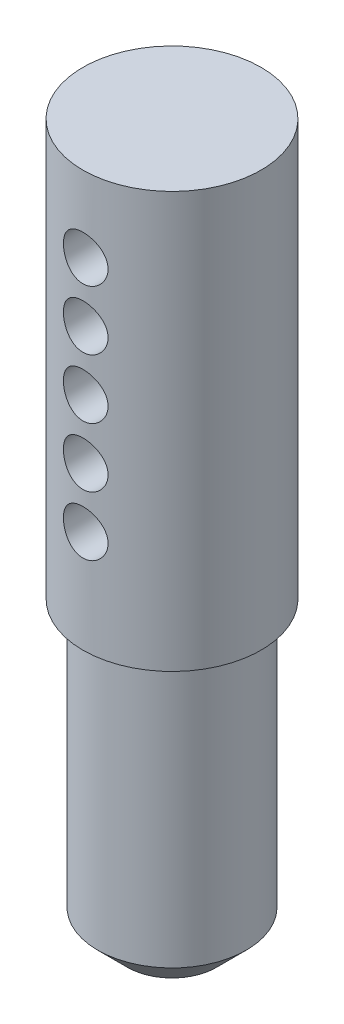
SolidWorks part; units mm, degrees
material "Plain Carbon Steel"
ref_plane "Front" through (0, 0, 0) normal (0, 0, 1) x (1, 0, 0)
ref_plane "Top" through (0, 0, 0) normal (0, 1, 0) x (1, 0, 0)
ref_plane "Right" through (0, 0, 0) normal (1, 0, 0) x (0, 0, -1)
sketch "Sketch1" plane through (0, 0, 0) normal (0, 0, 1) x (1, 0, 0)
  line L0 (0, 76.0545) -> (0, -96.9835) construction
  line L1 (-81.8474, 0) -> (90.8169, 0) construction
  line L2 (0, 0) -> (9.525, 0)
  line L3 (9.525, 0) -> (9.525, -44.45)
  line L4 (9.525, -44.45) -> (7.9375, -44.45)
  line L5 (7.9375, -44.45) -> (7.9375, -73.025)
  line L6 (4.7625, -76.2) -> (0, -76.2)
  line L7 (0, -76.2) -> (0, 0)
  line L8 (7.9375, -73.025) -> (4.7625, -76.2)
  point P10 (7.9375, -76.2)
  dimension "D1" = 19.05
  dimension "D2" = 15.875
  dimension "D3" = 76.2
  dimension "D4" = 31.75
revolve "Revolve1" add sketch "Sketch1" angle 360 about L0
cosmetic thread "Cosmetic Thread1"
cosmetic thread "Cosmetic Thread2"
cosmetic thread "Cosmetic Thread3"
sketch "Sketch2" plane through (0, 0, 0) normal (0, 0, 1) x (1, 0, 0)
  line L0 (-4.7625, -76.2) -> (4.7625, -76.2) construction
  circle A0 centre (0, -8.128) radius 2.3876
  circle A1 centre (0, -14.478) radius 2.3876
  circle A2 centre (0, -20.828) radius 2.3876
  circle A3 centre (0, -27.178) radius 2.3876
  circle A4 centre (0, -33.528) radius 2.3876
  dimension "D1" = 4.7752
  dimension "D2" = 6.35
  dimension "D3" = 6.35
  dimension "D4" = 6.35
  dimension "D5" = 6.35
  dimension "D6" = 42.672
extrude "Cut-Extrude1" cut sketch "Sketch2" against normal mid plane 36.322
